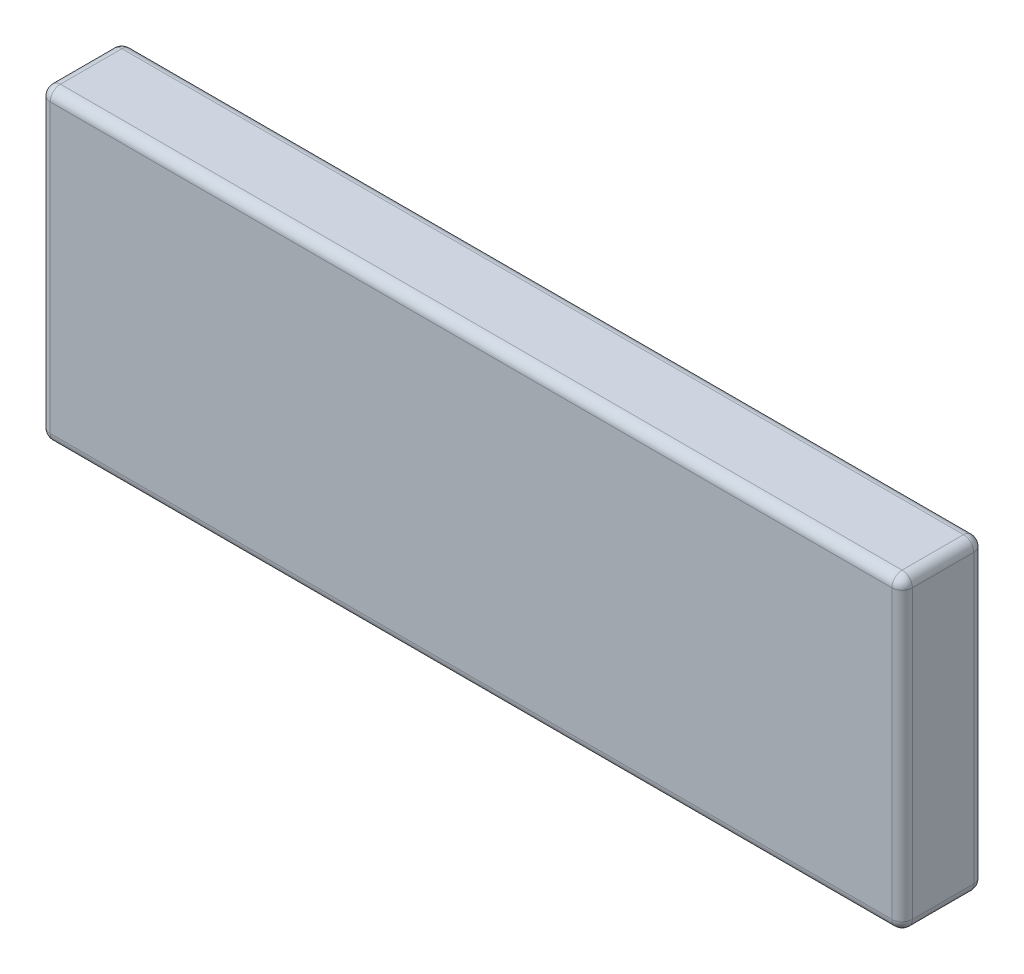
SolidWorks part; units mm, degrees
ref_plane "Front Plane" through (0, 0, 0) normal (0, 0, 1) x (1, 0, 0)
ref_plane "Top Plane" through (0, 0, 0) normal (0, 1, 0) x (1, 0, 0)
ref_plane "Right Plane" through (0, 0, 0) normal (1, 0, 0) x (0, 0, -1)
sketch "Sketch2" plane through (0, 0, 0) normal (0, 0, 1) x (1, 0, 0)
  line L1 (0, 0) -> (84.1976, 0)
  line L2 (0, 0) -> (0, -30.0432)
  line L3 (0, -30.0432) -> (84.1976, -30.0432)
  line L4 (84.1976, 0) -> (84.1976, -30.0432)
extrude "Boss-Extrude1" add sketch "Sketch2" along normal blind 8
sketch "Sketch3" plane through (0, 0, 0) normal (-1, 0, 0) x (0, 0, 1)
  line L0 (4.236, -25.5479) -> (4.236, -18.7161) construction
  line L1 (2.916, -25.5479) -> (2.916, -18.7161)
  line L2 (5.5559, -25.5479) -> (5.5559, -18.7161)
  arc A0 (2.916, -25.5479) -> (5.5559, -25.5479) centre (4.236, -25.5479) ccw
  arc A1 (5.5559, -18.7161) -> (2.916, -18.7161) centre (4.236, -18.7161) ccw
  circle A2 centre (4.236, -13.7075) radius 1.591
  point P2 (4.236, -22.132)
sketch "Sketch4" plane through (0, 0, 0) normal (-1, 0, 0) x (0, 0, 1)
  line L0 (4.1545, -7.4853) -> (4.1545, -4.1531) construction
  line L1 (3.34, -7.4853) -> (3.34, -4.1531)
  line L2 (4.969, -7.4853) -> (4.969, -4.1531)
  arc A0 (3.34, -7.4853) -> (4.969, -7.4853) centre (4.1545, -7.4853) ccw
  arc A1 (4.969, -4.1531) -> (3.34, -4.1531) centre (4.1545, -4.1531) ccw
  point P2 (4.1545, -5.8192)
  point P7 (4.236, -7.4853)
  point P8 (4.1545, -4.1531)
fillet "Fillet5" radius 1 12 edges at (84.1976, -30.0432, 4) (84.1976, 0, 4) (42.0988, 0, 8) (0, 0, 4) (42.0988, -30.0432, 8) (0, -15.0216, 8) (0, -30.0432, 4) (42.0988, 0, 0) (0, -15.0216, 0) (84.1976, -15.0216, 0) (84.1976, -15.0216, 8) (42.0988, -30.0432, 0)
